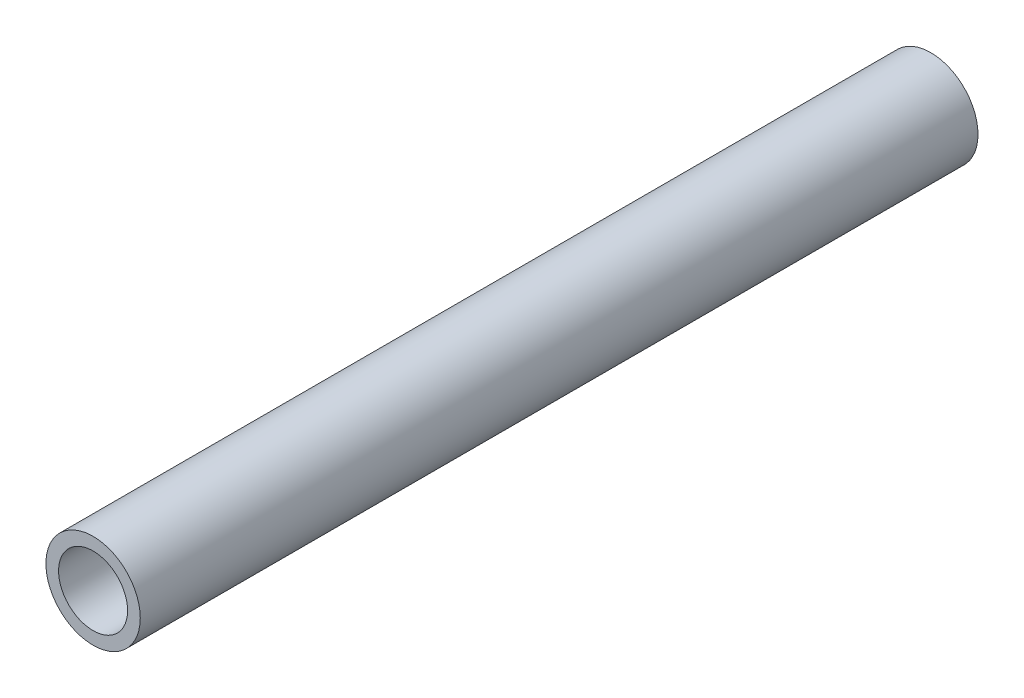
SolidWorks part; units mm, degrees
material "PVC Rígido"
ref_plane "Alzado" through (0, 0, 0) normal (0, 0, 1) x (1, 0, 0)
ref_plane "Planta" through (0, 0, 0) normal (0, 1, 0) x (1, 0, 0)
ref_plane "Vista lateral" through (0, 0, 0) normal (1, 0, 0) x (0, 0, -1)
sketch "Croquis1" plane through (0, 0, 0) normal (0, 0, 1) x (1, 0, 0)
  circle A0 centre (0, 0) radius 10.7
  circle A1 centre (0, 0) radius 7.825
  dimension "D1" = 21.4
  dimension "D2" = 15.65
extrude "Saliente-Extruir1" add sketch "Croquis1" along normal mid plane 190
